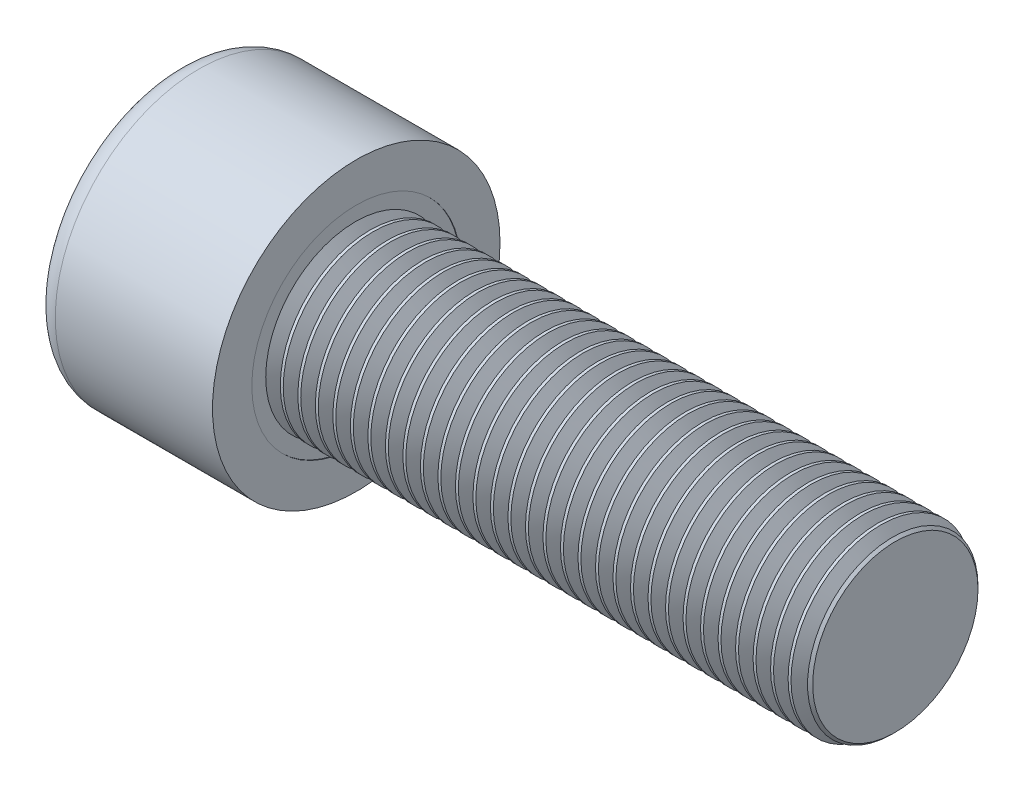
SolidWorks part; units mm, degrees
ref_plane "Front" through (0, 0, 0) normal (0, 0, 1) x (1, 0, 0)
ref_plane "Top" through (0, 0, 0) normal (0, 1, 0) x (1, 0, 0)
ref_plane "Right" through (0, 0, 0) normal (1, 0, 0) x (0, 0, -1)
sketch "Sketch1" plane through (0, 0, 0) normal (1, 0, 0) x (0, 0, -1)
  circle A0 centre (0, 0) radius 8
  dimension "dk" = 16
extrude "BaseHead" add sketch "Sketch1" along normal blind 10
sketch "Sketch2" plane through (10, 0, 0) normal (1, 0, 0) x (0, 0, -1)
  circle A0 centre (0, 0) radius 5
  dimension "d" = 10
extrude "BaseBody" add sketch "Sketch2" along normal blind 30
cosmetic thread "ThreadCosmetic1" [suppressed] parameters "b"=30, "D2"=8.376
sketch "Sketch3" plane through (0, 0, 0) normal (1, 0, 0) x (0, 0, -1)
  line L1 (4.6188, 0) -> (2.3094, 4)
  line L2 (2.3094, 4) -> (-2.3094, 4)
  line L3 (-2.3094, 4) -> (-4.6188, 0)
  line L4 (-4.6188, 0) -> (-2.3094, -4)
  line L5 (-2.3094, -4) -> (2.3094, -4)
  line L6 (2.3094, -4) -> (4.6188, 0)
  circle A0 centre (0, 0) radius 4 construction
  dimension "s" = 8
  dimension "e" = 9.2376
extrude "HexagonSocket" cut sketch "Sketch3" along normal blind 5
sketch "Sketch4" plane through (-4.1961, 0.75, 0) normal (0, 0, 1) x (-1, 0, 0)
  line L0 (-9.1961, 4.75) -> (-11.5055, 0.75)
  line L2 (-11.5055, 0.75) -> (-9.1961, 0.75)
  line L3 (-9.1961, 0.75) -> (-9.1961, 4.75)
  line L4 (-5.0351, 0.75) -> (0.839, 0.75) construction
  line L5 (-44.1961, 0.75) -> (-14.1961, 0.75) construction
  line L6 (-14.1961, 0.75) -> (-4.1961, 0.75) construction
  dimension "m" = 60
revolve "Cut-Revolve1" cut sketch "Sketch4" angle 360 about L4
fillet "HeadFillet" [suppressed] radius 0.4
fillet "TopFillet" radius 1.25 1 edges at (0, 0, -8)
chamfer "Chamfer1" distance 0.4 angle 45 1 edges at (40, 0, -5)
sketch "Sketch5" plane through (0, 0, 0) normal (0, 0, 1) x (1, 0, 0)
  line L0 (39.6, 4.2968) -> (40.006, 5)
  line L1 (40.006, 5) -> (40.006, 5.812)
  line L2 (40.006, 5.812) -> (39.194, 5.812)
  line L3 (39.194, 5.812) -> (39.194, 5)
  line L4 (39.194, 5) -> (39.6, 4.2968)
  line L5 (0, 0) -> (7.8886, 0) construction
  line L6 (39.6, -5) -> (39.6, 5) construction
  dimension "D1" = 10
  dimension "D2" = 0.812
revolve "Cut-Revolve10" cut sketch "Sketch5" angle 360 about L5
pattern_linear "LPattern10" count 31 spacing 0.9744 along (-1, 0, 0) of "Cut-Revolve10"
equation "\"r1@TopFillet\" = \"d@Sketch2\" / 8"
equation "\"D1@Chamfer1\" = \"r@HeadFillet\""
equation "\"D1@Sketch5\" = \"d@Sketch2\""
equation "\"D2@Sketch5\" =  ( \"d@Sketch2\" - \"D2@ThreadCosmetic1\" )  / 2"
equation "\"D3@LPattern10\" = \"D2@Sketch5\" * 1.2"
equation "\"D1@LPattern10\" = \"b@ThreadCosmetic1\" / \"D3@LPattern10\""
